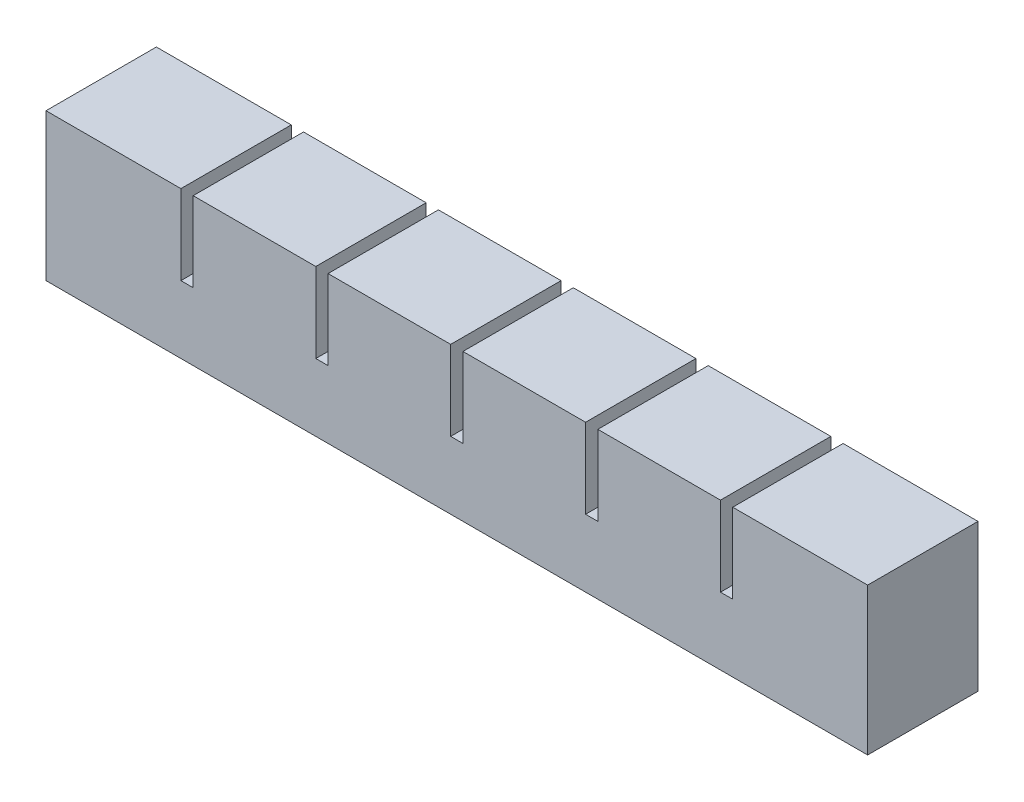
SolidWorks part; units mm, degrees
ref_plane "Front Plane" through (0, 0, 0) normal (0, 0, 1) x (1, 0, 0)
ref_plane "Top Plane" through (0, 0, 0) normal (0, 1, 0) x (1, 0, 0)
ref_plane "Right Plane" through (0, 0, 0) normal (1, 0, 0) x (0, 0, -1)
sketch "Sketch1" plane through (0, 0, 0) normal (0, 0, 1) x (1, 0, 0)
  line L1 (0, 0) -> (20, 0)
  line L2 (0, 0) -> (0, 18)
  line L3 (0, 18) -> (20, 18)
  line L4 (20, 0) -> (20, 18)
  dimension "D1" = 20
  dimension "D2" = 18
extrude "Boss-Extrude1" add sketch "Sketch1" along normal blind 18
sketch "Sketch2" plane through (0, 0, 0) normal (0, -1, 0) x (1, 0, 0)
  line L0 (20, 18) -> (20, 0) construction
  line L1 (5, 13) -> (15, 13)
  line L2 (5, 13) -> (5, 5)
  line L3 (5, 5) -> (15, 5)
  line L4 (15, 13) -> (15, 5)
  line L5 (0, 18) -> (20, 18) construction
  line L6 (0, 18) -> (0, 0) construction
  line L7 (0, 0) -> (20, 0) construction
  dimension "D1" = 5
  dimension "D2" = 5
  dimension "D3" = 5
  dimension "D4" = 5
extrude "Cut-Extrude1" cut sketch "Sketch2" against normal blind 13
sketch "Sketch3" plane through (20, 0, 0) normal (1, 0, 0) x (0, 0, -1)
  line L0 (0, 0) -> (0, 18) construction
  line L1 (-18, 0) -> (0, 0)
  line L2 (-18, 0) -> (-18, 5)
  line L3 (-18, 5) -> (0, 5)
  line L4 (0, 0) -> (0, 5)
  dimension "D1" = 5
extrude "Boss-Extrude2" add sketch "Sketch3" along normal blind 2
pattern_linear "LPattern1" count 6 spacing 22 along (1, 0, 0) of bodies 103
combine bodies "Combine1" operation type add bodies to combine 104 103 106 107 108 105
sketch "Sketch4" plane through (130, 0, 0) normal (1, 0, 0) x (0, 0, -1)
  line L1 (-18, 5) -> (0, 5)
  line L2 (-18, 5) -> (-18, 18)
  line L3 (-18, 18) -> (0, 18)
  line L4 (0, 5) -> (0, 18)
extrude "Boss-Extrude3" add sketch "Sketch4" along normal up to surface (2 mm away) up to face at (132, 2.5, 9)
sketch "Sketch5" plane through (0, 0, 0) normal (-1, 0, 0) x (0, 0, 1)
  line L1 (0, 18) -> (18, 18)
  line L2 (0, 18) -> (0, 0)
  line L3 (0, 0) -> (18, 0)
  line L4 (18, 18) -> (18, 0)
extrude "Boss-Extrude4" add sketch "Sketch5" along normal blind 2
ref_point "Point1"
sketch "Sketch6" plane through (0, 0, 0) normal (0, -1, 0) x (-1, 0, 0)
  line L0 (-125, -5) -> (-125, -13) construction
  line L1 (-5, -8) -> (-125, -8)
  line L2 (-5, -8) -> (-5, -10)
  line L3 (-5, -10) -> (-125, -10)
  line L4 (-125, -8) -> (-125, -10)
  line L5 (-5, -8) -> (-125, -10) construction
  line L6 (-5, -10) -> (-125, -8) construction
  point P0 (-65, -9)
  dimension "D1" = 2
extrude "Cut-Extrude2" cut sketch "Sketch6" against normal blind 2
sketch "Sketch7" plane through (0, 0, 0) normal (0, -1, 0) x (-1, 0, 0)
  line L1 (2, -18) -> (-132, -18)
  line L2 (2, -18) -> (2, 0)
  line L3 (2, 0) -> (-132, 0)
  line L4 (-132, -18) -> (-132, 0)
extrude "Boss-Extrude5" add sketch "Sketch7" along normal blind 6
